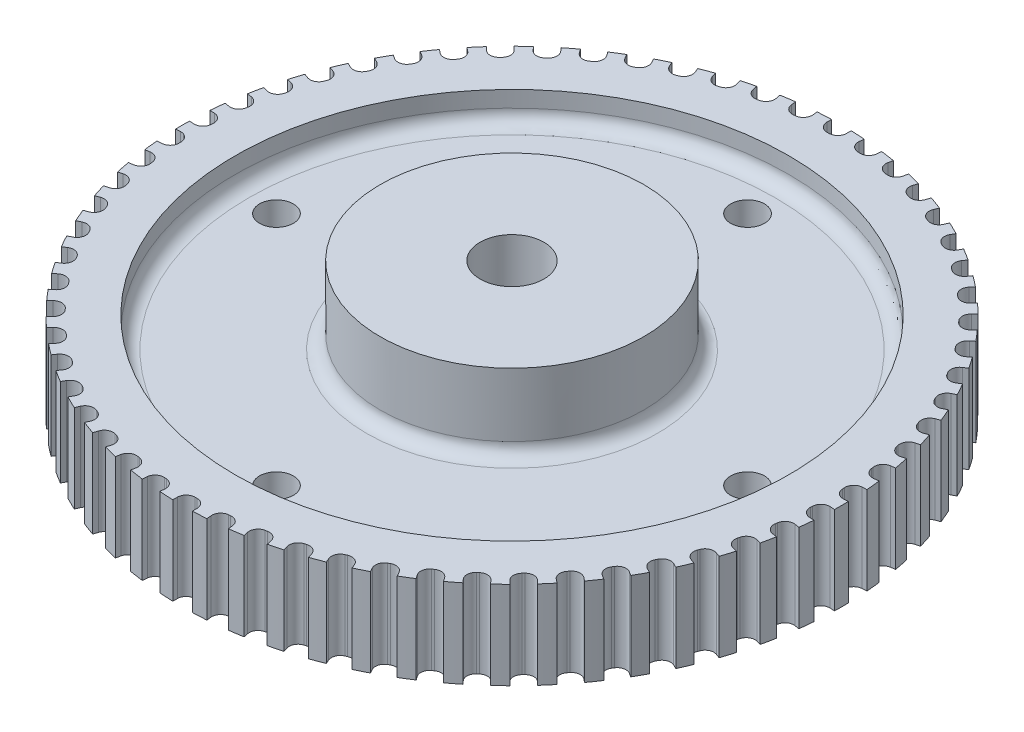
SolidWorks part; units mm, degrees
ref_plane "Plano frontal" through (0, 0, 0) normal (0, 0, 1) x (1, 0, 0)
ref_plane "Plano superior" through (0, 0, 0) normal (0, 1, 0) x (1, 0, 0)
ref_plane "Plano direito" through (0, 0, 0) normal (1, 0, 0) x (0, 0, -1)
sketch "Esboço1" plane through (0, 0, 0) normal (0, 0, 1) x (1, 0, 0)
  line L0 (0, 0) -> (0, 7.4765) construction
  line L1 (4.725, 0) -> (4.725, 20)
  line L2 (4.725, 20) -> (19.5, 20)
  line L3 (19.5, 20) -> (19.5, 8.6)
  line L4 (19.5, 8.6) -> (40.925, 8.6)
  line L5 (40.925, 8.6) -> (40.925, 13)
  line L6 (40.925, 13) -> (48.75, 13)
  line L7 (48.75, 13) -> (48.75, 0)
  line L8 (48.75, 0) -> (40.925, 0)
  line L9 (40.925, 0) -> (40.925, 4.5)
  line L10 (40.925, 4.5) -> (19.5, 4.5)
  line L11 (19.5, 4.5) -> (19.5, 0)
  line L12 (19.5, 0) -> (4.725, 0)
  line L13 (0, 0) -> (4.725, 0) construction
  point P14 (48.75, 6.5)
  dimension "D1" = 9.45
  dimension "D2" = 39
  dimension "D3" = 20
  dimension "D4" = 81.85
  dimension "D5" = 13
  dimension "D6" = 97.5
  dimension "D7" = 11.4
  dimension "D8" = 4.5
revolve "Revolução1" add sketch "Esboço1" angle 360 about L0
fillet "Filete1" radius 2 4 edges at (0, 4.5, -40.925) (0, 4.5, -19.5) (0, 8.6, -19.5) (0, 8.6, -40.925)
sketch "Esboço2" plane through (0, 0, 0) normal (0, 1, 0) x (1, 0, 0)
  line L0 (0, 34.85) -> (0, -34.85) construction
  line L1 (-34.85, 0) -> (34.85, 0) construction
  circle A0 centre (0, 34.85) radius 2.5
  circle A1 centre (0, -34.85) radius 2.5
  circle A2 centre (34.85, 0) radius 2.5
  circle A3 centre (-34.85, 0) radius 2.5
  point P5 (0, 0)
  point P6 (0, 0)
  point P12 (0, 37.35)
  point P13 (0, -37.35)
  dimension "D1" = 5
  dimension "D2" = 74.7
extrude "Corte-extrusão1" cut sketch "Esboço2" along normal through all
sketch "Esboço3" plane through (0, 13, 0) normal (0, 1, 0) x (1, 0, 0)
  line L0 (0, 34.85) -> (0, 51.6619) construction
  line L2 (-1.45, 50.5672) -> (1.45, 50.5672)
  line L3 (-1.45, 50.5672) -> (-1.45, 48.05)
  line L4 (-0.15, 46.75) -> (0.15, 46.75)
  line L5 (1.45, 50.5672) -> (1.45, 48.05)
  circle A0 centre (0, 0) radius 46.75 construction
  arc A1 (0.15, 46.75) -> (1.45, 48.05) centre (0.15, 48.05) ccw
  arc A2 (-1.45, 48.05) -> (-0.15, 46.75) centre (-0.15, 48.05) ccw
  point P10 (0, 50.5672)
  dimension "D1" = 93.5
  dimension "D3" = 1.3
  dimension "D2" = 2.9
extrude "Corte-extrusão2" cut sketch "Esboço3" against normal through all
pattern_circular "PadrãoCircular1" count 62 over 360 about axis through (0, 0, 0) along (0, 1, 0) of "Corte-extrusão2"
